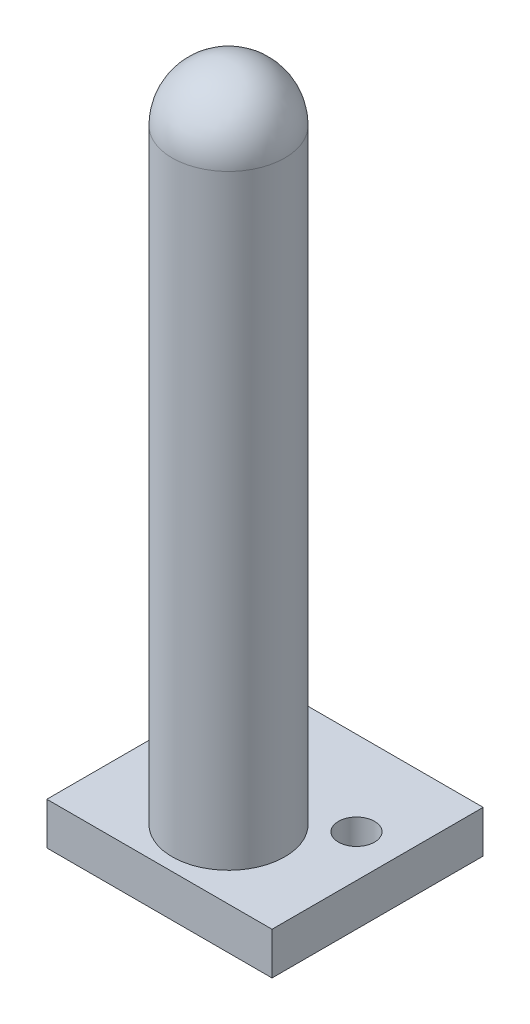
SolidWorks part; units mm, degrees
ref_plane "Front Plane" through (0, 0, 0) normal (0, 0, 1) x (1, 0, 0)
ref_plane "Top Plane" through (0, 0, 0) normal (0, 1, 0) x (1, 0, 0)
ref_plane "Right Plane" through (0, 0, 0) normal (1, 0, 0) x (0, 0, -1)
sketch "Sketch1" plane through (0, 0, 0) normal (0, 0, 1) x (1, 0, 0)
  line L0 (0, 39.761) -> (0, -42.6267) construction
  line L1 (-8, 20.0841) -> (8, 20.0841)
  line L2 (8, 20.0841) -> (8, 23.0841)
  line L3 (8, 23.0841) -> (-8, 23.0841)
  line L4 (-8, 20.0841) -> (-8, 23.0841)
  point P11 (0, 23.0841)
  point P12 (0, 20.0841)
  dimension "D1" = 8
  dimension "D2" = 3
extrude "Boss-Extrude1" add sketch "Sketch1" along normal blind 15
sketch "Sketch2" plane through (0, 23.0841, 0) normal (0, 1, 0) x (1, 0, 0)
  line L0 (0, -13.2843) -> (0, 2.1329) construction
  line L1 (8, 0) -> (-8, 0) construction
  circle A0 centre (5, -6) radius 1.2826
  circle A1 centre (-5, -6) radius 1.2826
  dimension "D1" = 5
  dimension "D2" = 6
extrude "Cut-Extrude1" cut sketch "Sketch2" against normal blind 12
sketch "Sketch3" plane through (0, 23.0841, 0) normal (0, 1, 0) x (1, 0, 0)
  circle A0 centre (0, -10.0923) radius 4
  point P2 (0, -9.2438)
  point P3 (0, -10.0923)
extrude "Boss-Extrude2" add sketch "Sketch3" along normal blind 43
sketch "Sketch5" plane through (0, 66.0841, 0) normal (0, 1, 0) x (1, 0, 0)
  line L0 (0, -6.0923) -> (0, -14.0923) construction
  circle A0 centre (0, -10.0923) radius 4 construction
  circle A1 centre (0, -10.0923) radius 4 construction
revolve "Revolve1" add sketch "Sketch5" angle 360 about L0
